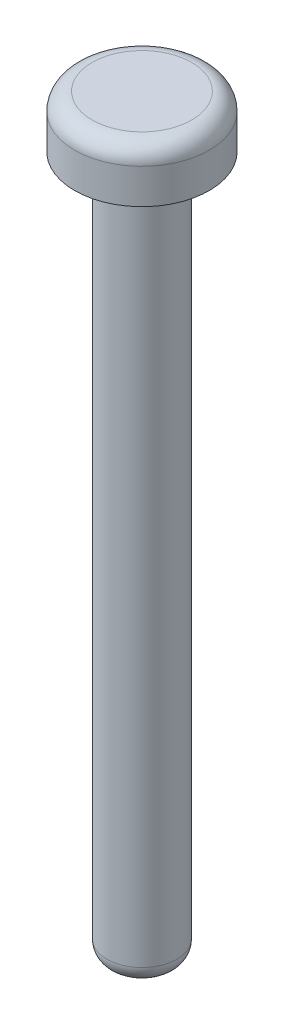
SolidWorks part; units mm, degrees
ref_plane "Спереди" through (0, 0, 0) normal (0, 0, 1) x (1, 0, 0)
ref_plane "Сверху" through (0, 0, 0) normal (0, 1, 0) x (1, 0, 0)
ref_plane "Справа" through (0, 0, 0) normal (1, 0, 0) x (0, 0, -1)
sketch "Sketch1" plane through (0, 0, 0) normal (0, 1, 0) x (1, 0, 0)
  circle A0 centre (0, 0) radius 2
  dimension "D1" = 4
extrude "Boss-Extrude1" add sketch "Sketch1" along normal blind 40
sketch "Sketch2" plane through (0, 40, 0) normal (0, 1, 0) x (1, 0, 0)
  circle A0 centre (0, 0) radius 3.85
  dimension "D1" = 7.7
extrude "Boss-Extrude2" add sketch "Sketch2" along normal blind 3
fillet "Fillet1" radius 1 1 edges at (0, 43, 3.85)
fillet "Fillet2" radius 1 2 edges at (0, 0, 2) (0, 40, 2)
